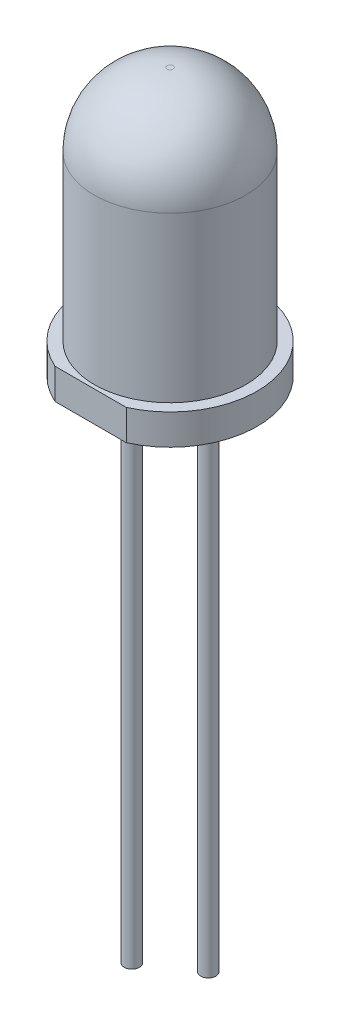
SolidWorks part; units mm, degrees
material "Perspex (TM) GS Acrylic Cast Sheet"
ref_plane "Front Plane" through (0, 0, 0) normal (0, 0, 1) x (1, 0, 0)
ref_plane "Top Plane" through (0, 0, 0) normal (0, 1, 0) x (1, 0, 0)
ref_plane "Right Plane" through (0, 0, 0) normal (1, 0, 0) x (0, 0, -1)
sketch "Sketch1" plane through (0, 0, 0) normal (0, 0, 1) x (1, 0, 0)
  line L0 (0, 0) -> (0, 8.75)
  line L1 (0, 0) -> (2.85, 0)
  line L2 (2.85, 0) -> (2.85, 1)
  line L3 (2.85, 1) -> (2.48, 1)
  line L4 (2.48, 1) -> (2.48, 6.37)
  line L5 (0, 8.75) -> (0.1, 8.75)
  arc A0 (2.48, 6.37) -> (0.1, 8.75) centre (0.1, 6.37) ccw
  dimension "D5" = 0.1
  dimension "D1" = 8.75
  dimension "D2" = 2.85
  dimension "D3" = 2.48
  dimension "D4" = 1
revolve "Revolve1" add sketch "Sketch1" angle 360 about L0
sketch "Sketch2" plane through (0, 0, 0) normal (0, -1, 0) x (1, 0, 0)
  line L0 (0, 0) -> (0, 2.6) construction
  line L1 (-1.1673, 2.6) -> (1.1673, 2.6)
  line L2 (0, 2.6) -> (0, 2.85) construction
  line L3 (0, 0) -> (0, -2.85) construction
  circle A0 centre (0, 0) radius 2.85 construction
  arc A1 (1.1673, 2.6) -> (-1.1673, 2.6) centre (0, 0) ccw
  dimension "D1" = 5.45
extrude "Cut-Extrude1" cut sketch "Sketch2" against normal up to surface (1 mm away) up to face at (0, 1, -2.48)
sketch "Sketch3" plane through (0, 0, 0) normal (0, -1, 0) x (1, 0, 0)
  line L0 (0, 1.25) -> (0, -1.25) construction
  circle A0 centre (0, -1.25) radius 0.25
  circle A1 centre (0, 1.25) radius 0.25
  dimension "D2" = 0.5
  dimension "D1" = 2.5
extrude "Boss-Extrude1" add sketch "Sketch3" along normal blind 16
sketch "Sketch4" plane through (0, -16, 0) normal (0, -1, 0) x (1, 0, 0)
  circle A0 centre (0, -1.25) radius 0.25 construction
  circle A1 centre (0, -1.25) radius 0.25
  circle A2 centre (0, 1.25) radius 0.25 construction
  circle A3 centre (0, 1.25) radius 0.25 construction
extrude "Boss-Extrude2" add sketch "Sketch4" along normal blind 1.5
